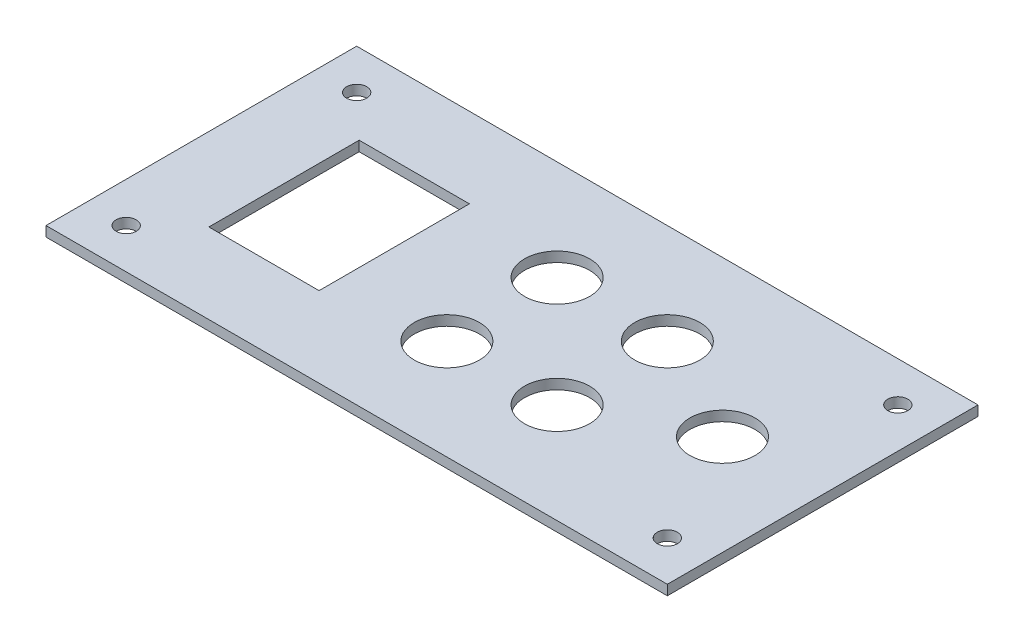
SolidWorks part; units mm, degrees
ref_plane "Front Plane" through (0, 0, 0) normal (0, 0, 1) x (1, 0, 0)
ref_plane "Top Plane" through (0, 0, 0) normal (0, 1, 0) x (1, 0, 0)
ref_plane "Right Plane" through (0, 0, 0) normal (1, 0, 0) x (0, 0, -1)
sketch "Sketch1" plane through (0, 0, 0) normal (0, 1, 0) x (1, 0, 0)
  line L0 (-104.281, 0) -> (104.281, 0) construction
  line L2 (-32.5, 16) -> (-7.5, 16) construction
  line L3 (-32.5, 16) -> (-32.5, -16) construction
  line L4 (-32.5, -16) -> (-7.5, -16) construction
  line L5 (-7.5, 16) -> (-7.5, -16) construction
  line L6 (-31, 15) -> (-9, 15)
  line L7 (-31, 15) -> (-31, -15)
  line L8 (-31, -15) -> (-9, -15)
  line L9 (-9, 15) -> (-9, -15)
  line L10 (-31, 15) -> (-9, -15) construction
  line L11 (-31, -15) -> (-9, 15) construction
  line L12 (-32.5, 16) -> (-7.5, -16) construction
  line L13 (-32.5, -16) -> (-7.5, 16) construction
  line L14 (-47.5, 31) -> (76.5, 31)
  line L15 (-47.5, 31) -> (-47.5, -31)
  line L16 (-47.5, -31) -> (76.5, -31)
  line L17 (76.5, 31) -> (76.5, -31)
  circle A0 centre (12.5, 11) radius 6.5
  circle A1 centre (12.5, 11) radius 9 construction
  circle A2 centre (12.5, -11) radius 9 construction
  circle A4 centre (12.5, -11) radius 6.5
  circle A6 centre (34.5, 11) radius 6.5
  circle A8 centre (34.5, -11) radius 6.5
  circle A10 centre (34.5, 11) radius 9 construction
  circle A11 centre (34.5, -11) radius 9 construction
  circle A12 centre (56.5, 0) radius 9 construction
  circle A13 centre (56.5, 0) radius 6.5
  circle A14 centre (-39.5, 23) radius 2
  circle A15 centre (68.5, 23) radius 2
  circle A16 centre (68.5, -23) radius 2
  circle A17 centre (-39.5, -23) radius 2
  point P6 (0, 0)
  point P8 (-20, 0)
  point P13 (0, 0)
  point P20 (22, 0)
  point P21 (22, 0)
  point P23 (-20, 0)
  point P36 (65.5, 0)
  point P37 (3.5, 11)
  point P38 (12.5, 20)
  point P43 (0, 0)
  point P44 (0, 0)
  dimension "D1" = 13
  dimension "D2" = 18
  dimension "D17" = 18
  dimension "D18" = 13
  dimension "D19" = 4
  dimension "D4" = 22
  dimension "D5" = 30
  dimension "D6" = 20
  dimension "D3" = 22
  dimension "D7" = 11
  dimension "D9" = 22
  dimension "D10" = 25
  dimension "D11" = 32
  dimension "D12" = 15
  dimension "D13" = 15
  dimension "D14" = 11
  dimension "D15" = 15
  dimension "D16" = 11
  dimension "D20" = 8
  dimension "D21" = 8
  dimension "D22" = 8
  dimension "D8" = 2
extrude "Boss-Extrude1" add sketch "Sketch1" along normal blind 2
